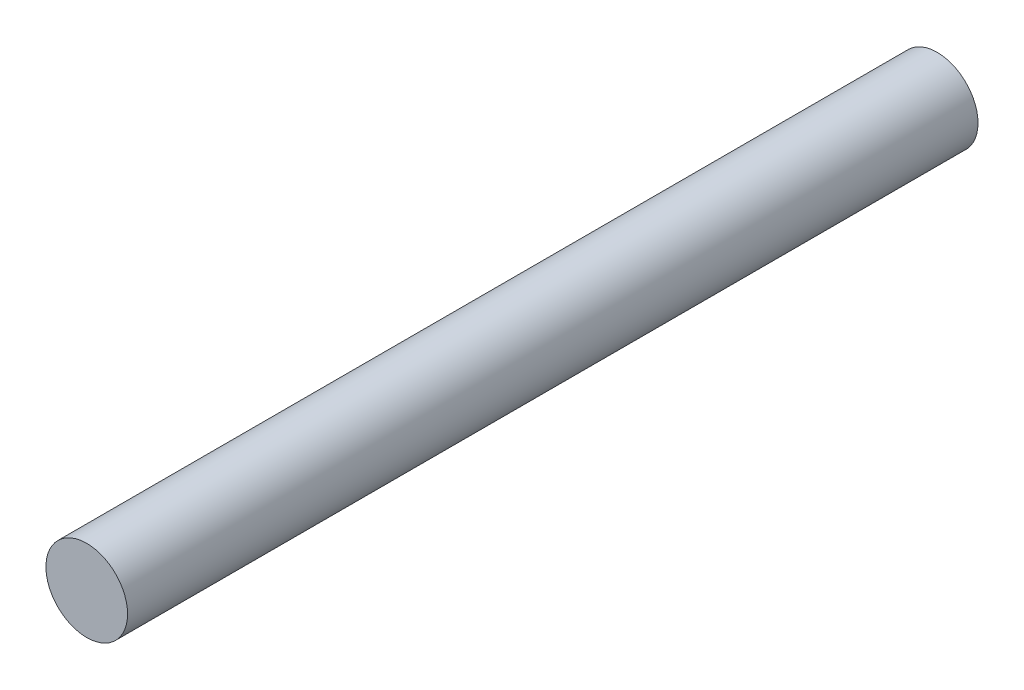
SolidWorks part; units mm, degrees
ref_plane "Front Plane" through (0, 0, 0) normal (0, 0, 1) x (1, 0, 0)
ref_plane "Top Plane" through (0, 0, 0) normal (0, 1, 0) x (1, 0, 0)
ref_plane "Right Plane" through (0, 0, 0) normal (1, 0, 0) x (0, 0, -1)
sketch "Sketch1" plane through (0, 0, 0) normal (0, 0, 1) x (1, 0, 0)
  circle A0 centre (0, 0) radius 24
  dimension "D1" = 48
extrude "Boss-Extrude1" add sketch "Sketch1" along normal blind 500
